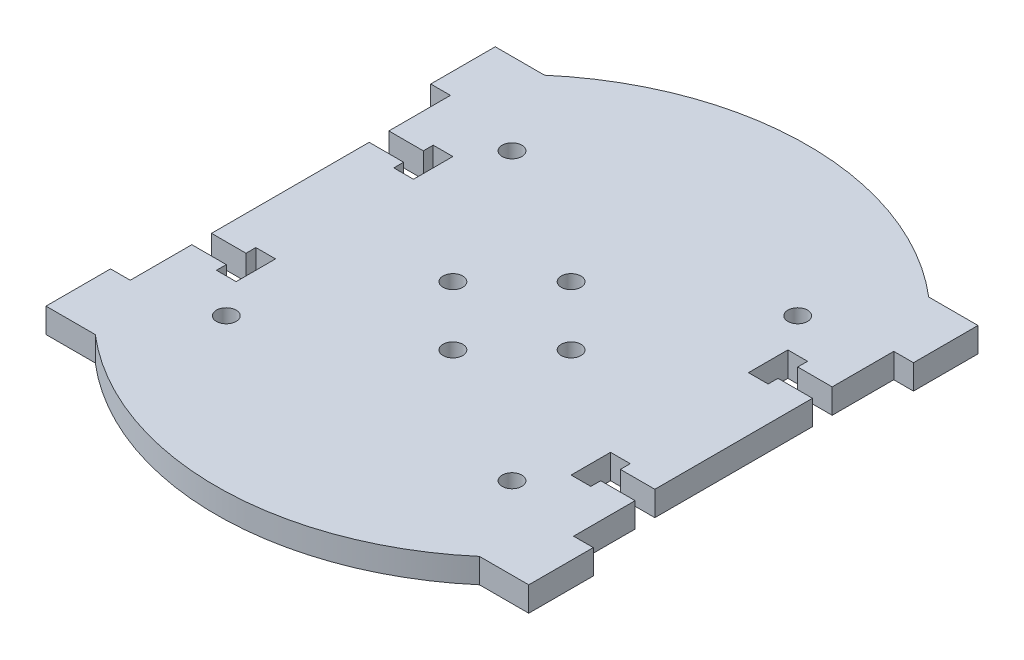
SolidWorks part; units mm, degrees
ref_plane "Front Plane" through (0, 0, 0) normal (0, 0, 1) x (1, 0, 0)
ref_plane "Top Plane" through (0, 0, 0) normal (0, 1, 0) x (1, 0, 0)
ref_plane "Right Plane" through (0, 0, 0) normal (1, 0, 0) x (0, 0, -1)
sketch "Sketch1" plane through (0, 0, 0) normal (0, 1, 0) x (1, 0, 0)
  line L0 (0, 0) -> (12, 0) construction
  line L5 (0, 0) -> (0, -60) construction
  line L7 (-49, 45.6) -> (-49, 32.5)
  line L8 (-49, -45.6) -> (-39, -45.6)
  line L9 (49, 45.6) -> (49, 32.5)
  line L10 (0, -45.6) -> (0, 14) construction
  line L11 (-45, 0) -> (14, 0) construction
  line L12 (-49, 45.6) -> (-38.9954, 45.6)
  line L13 (38.9954, 45.6) -> (49, 45.6)
  line L15 (-49, -45.6) -> (-39, -45.6)
  line L16 (39, -45.6) -> (49, -45.6)
  line L17 (49, -45.6) -> (39, -45.6)
  line L18 (49, 32.5) -> (45, 32.5)
  line L19 (34, -14) -> (38, -14)
  line L20 (49, -32.5) -> (45, -32.5)
  line L21 (-49, 32.5) -> (-45, 32.5)
  line L22 (-45, 32.5) -> (-45, 20)
  line L23 (-45, -32.5) -> (-49, -32.5)
  line L24 (-49, -32.5) -> (-49, -45.6)
  line L25 (49, -32.5) -> (49, -45.6)
  line L26 (45, 16) -> (38, 16)
  line L27 (38, 16) -> (38, 14)
  line L28 (38, 14) -> (34, 14)
  line L29 (34, 14) -> (34, 22)
  line L30 (34, 22) -> (38, 22)
  line L31 (38, 22) -> (38, 20)
  line L32 (38, 20) -> (45, 20)
  line L33 (38, -14) -> (38, -16)
  line L34 (38, -16) -> (45, -16)
  line L35 (45, -16) -> (45, 16)
  line L36 (45, 20) -> (45, 32.5)
  line L37 (34, -14) -> (34, -22)
  line L38 (34, -22) -> (38, -22)
  line L39 (38, -22) -> (38, -20)
  line L40 (38, -20) -> (45, -20)
  line L41 (-45, 20) -> (-38, 20)
  line L42 (-38, 20) -> (-38, 22)
  line L43 (-38, 22) -> (-34, 22)
  line L44 (-34, 22) -> (-34, 14)
  line L45 (-34, 14) -> (-38, 14)
  line L46 (-38, 14) -> (-38, 16)
  line L47 (-38, 16) -> (-45, 16)
  line L48 (-45, -16) -> (-38, -16)
  line L49 (-38, -16) -> (-38, -14)
  line L50 (-38, -14) -> (-34, -14)
  line L51 (-34, -14) -> (-34, -22)
  line L52 (-34, -22) -> (-38, -22)
  line L53 (-38, -22) -> (-38, -20)
  line L54 (-38, -20) -> (-45, -20)
  line L55 (-45, 16) -> (-45, -16)
  line L56 (-45, -20) -> (-45, -32.5)
  line L57 (45, -32.5) -> (45, -20)
  line L59 (-29, 29) -> (29, 29) construction
  line L60 (-29, 29) -> (-29, -29) construction
  line L61 (-29, -29) -> (29, -29) construction
  line L62 (29, 29) -> (29, -29) construction
  line L63 (0, -29) -> (0, 29) construction
  line L64 (-29, 0) -> (29, 0) construction
  circle A0 centre (0, 0) radius 12 construction
  circle A1 centre (-12, 0) radius 2
  circle A2 centre (0, 0) radius 12 construction
  circle A3 centre (0, 12) radius 2
  circle A4 centre (0, 0) radius 12 construction
  circle A5 centre (12, 0) radius 2
  circle A6 centre (0, 0) radius 12 construction
  circle A7 centre (0, -12) radius 2
  arc A8 (-38.9954, 45.6) -> (38.9954, 45.6) centre (0, 0) cw
  arc A9 (-39, -45.6) -> (39, -45.6) centre (0, 0) ccw
  circle A10 centre (29, 29) radius 2
  circle A11 centre (29, -29) radius 2
  circle A12 centre (-29, -29) radius 2
  circle A13 centre (-29, 29) radius 2
  point P18 (0, 0)
  point P72 (0, 0)
  point P75 (0, 0)
  point P85 (0, 0)
  point P88 (0, 0)
  point P122 (0, 0)
  dimension "D1" = 24
  dimension "D2" = 4
  dimension "D3" = 4
  dimension "D9" = 60
  dimension "D10" = 10
  dimension "D12" = 4
  dimension "D13" = 7
  dimension "D33" = 7
  dimension "D51" = 4
  dimension "D4" = 91.2
  dimension "D5" = 98
  dimension "D6" = 60
  dimension "D7" = 10.0046
  dimension "D8" = 10.0046
  dimension "D11" = 10
  dimension "D14" = 4
  dimension "D15" = 65
  dimension "D16" = 13.1
  dimension "D17" = 13.1
  dimension "D18" = 2
  dimension "D19" = 4
  dimension "D20" = 12.5
  dimension "D21" = 4
  dimension "D22" = 8
  dimension "D23" = 4
  dimension "D24" = 2
  dimension "D25" = 7
  dimension "D26" = 32
  dimension "D27" = 7
  dimension "D28" = 2
  dimension "D29" = 7
  dimension "D30" = 2
  dimension "D31" = 2
  dimension "D32" = 8
  dimension "D34" = 2
  dimension "D35" = 4
  dimension "D36" = 8
  dimension "D37" = 4
  dimension "D38" = 2
  dimension "D39" = 12.5
  dimension "D40" = 12.5
  dimension "D41" = 4
  dimension "D42" = 4
  dimension "D43" = 4
  dimension "D44" = 4
  dimension "D45" = 8
  dimension "D46" = 4
  dimension "D47" = 7
  dimension "D48" = 2
  dimension "D49" = 4
  dimension "D50" = 58
  dimension "D52" = 65
  dimension "D53" = 4
extrude "Boss-Extrude1" add sketch "Sketch1" along normal blind 5 contours L8 A9 L16 L25 L20 L57 L40 L39 L38 L37 L19 L33 L34 L35 L26 L27 L28 L29 L30 L31 L32 L36 L18 L9 L13 A8 L12 L7 L21 L22 L41 L42 L43 L44 L45 L46 L47 L55 L48 L49 L50 L51 L52 L53 L54 L56 L23 L24 A13
